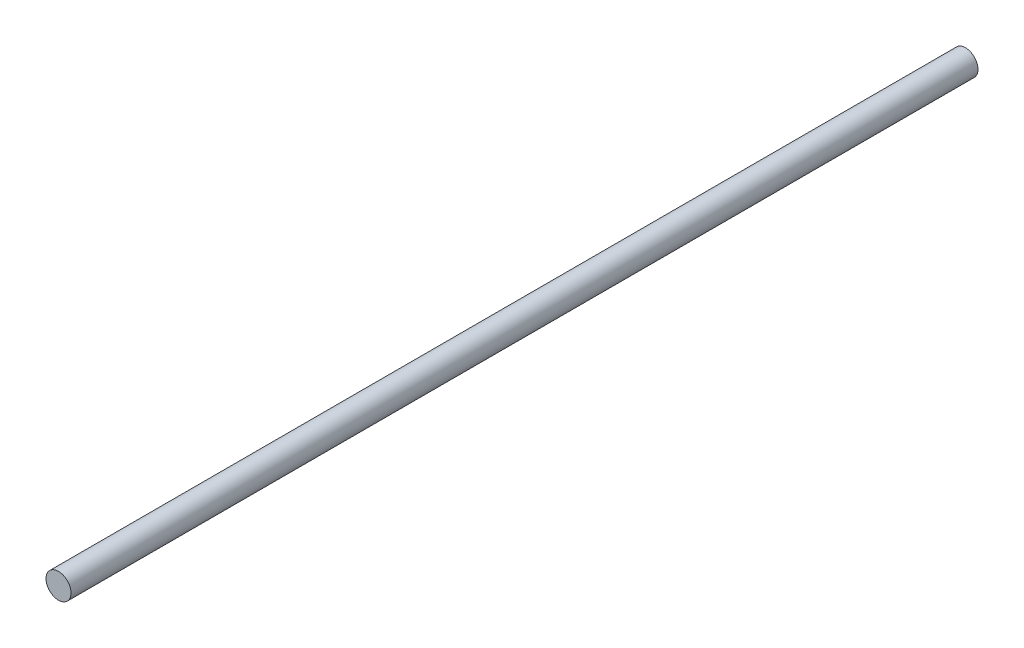
SolidWorks part; units mm, degrees
ref_plane "Plano frontal" through (0, 0, 0) normal (0, 0, 1) x (1, 0, 0)
ref_plane "Plano superior" through (0, 0, 0) normal (0, 1, 0) x (1, 0, 0)
ref_plane "Plano direito" through (0, 0, 0) normal (1, 0, 0) x (0, 0, -1)
sketch "Esboço1" plane through (0, 0, 0) normal (0, 0, 1) x (1, 0, 0)
  circle A0 centre (0, 0) radius 4
  dimension "D1" = 8
extrude "Ressalto-extrusão1" add sketch "Esboço1" along normal mid plane 290
